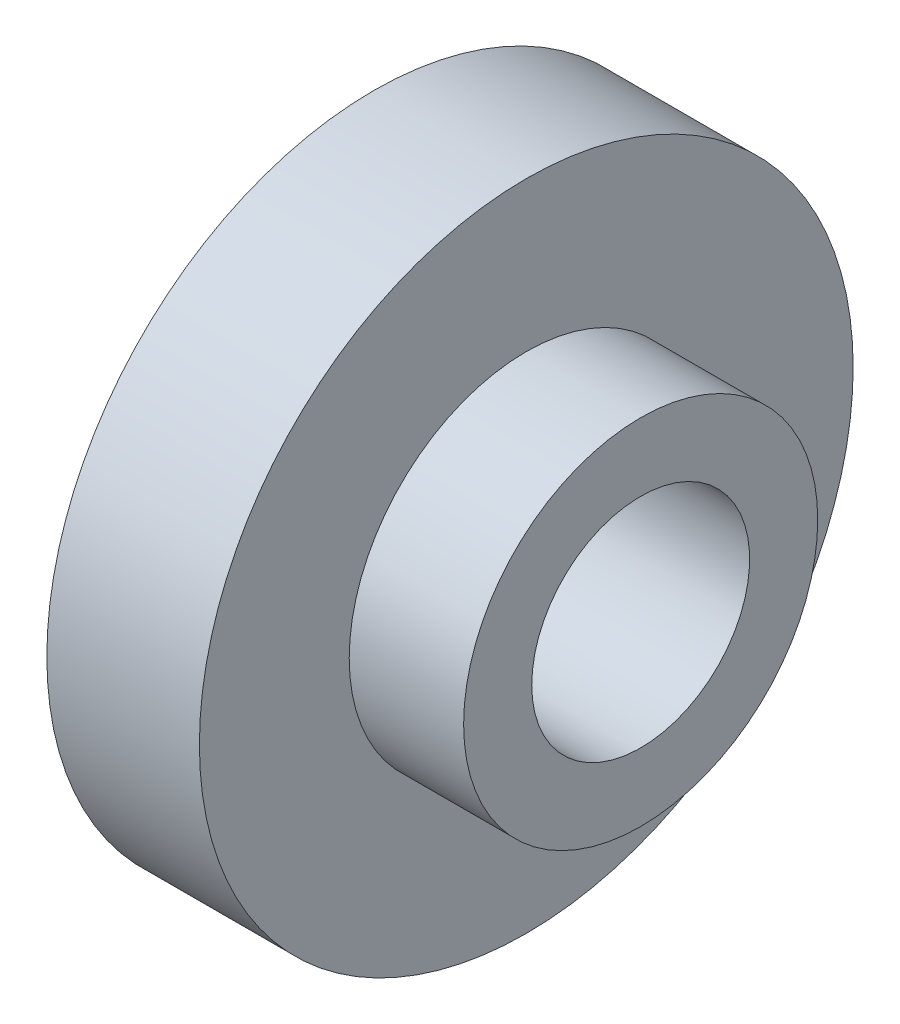
SolidWorks part; units mm, degrees
ref_plane "Front" through (0, 0, 0) normal (0, 0, 1) x (1, 0, 0)
ref_plane "Top" through (0, 0, 0) normal (0, 1, 0) x (1, 0, 0)
ref_plane "Right" through (0, 0, 0) normal (1, 0, 0) x (0, 0, -1)
sketch "Эскиз1" plane through (0, 0, 0) normal (0, 0, 1) x (1, 0, 0)
  line L0 (0, 0) -> (19.5817, 0) construction
  line L1 (0, 2.4) -> (0, 6)
  line L2 (0, 6) -> (2.8, 6)
  line L3 (2.8, 6) -> (2.8, 3.25)
  line L4 (2.8, 3.25) -> (4.9, 3.25)
  line L5 (4.9, 3.25) -> (4.9, 2)
  line L6 (4.9, 2) -> (0.4, 2)
  line L7 (0.4, 2) -> (0, 2.4)
  point P3 (0, 2)
  dimension "D1" = 4
  dimension "D2" = 12
  dimension "D3" = 6.5
  dimension "D4" = 4.9
  dimension "D5" = 2.8
  dimension "D8" = 0.4
revolve "Повернуть1" add sketch "Эскиз1" angle 360 about L0
